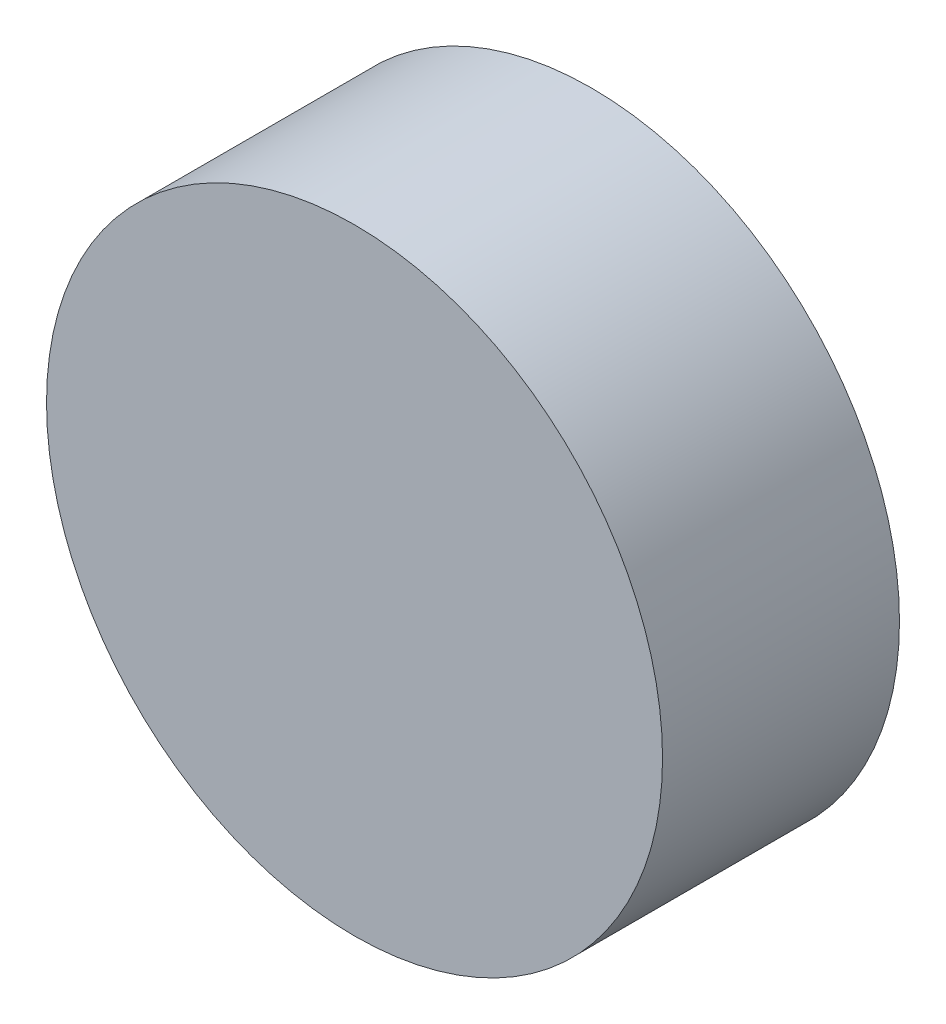
SolidWorks part; units mm, degrees
ref_plane "Front Plane" through (0, 0, 0) normal (0, 0, 1) x (1, 0, 0)
ref_plane "Top Plane" through (0, 0, 0) normal (0, 1, 0) x (1, 0, 0)
ref_plane "Right Plane" through (0, 0, 0) normal (1, 0, 0) x (0, 0, -1)
sketch "Sketch1" plane through (0, 0, 0) normal (0, 0, 1) x (1, 0, 0)
  circle A0 centre (0, 0) radius 33.02
  dimension "D1" = 66.04
extrude "Boss-Extrude1" add sketch "Sketch1" against normal blind 25.4
sketch "Sketch2" plane through (0, 0, -25.4) normal (0, 0, -1) x (-1, 0, 0)
  circle A0 centre (0, 0) radius 2.54
  dimension "D1" = 5.08
extrude "Cut-Extrude1" cut sketch "Sketch2" against normal blind 8.89
